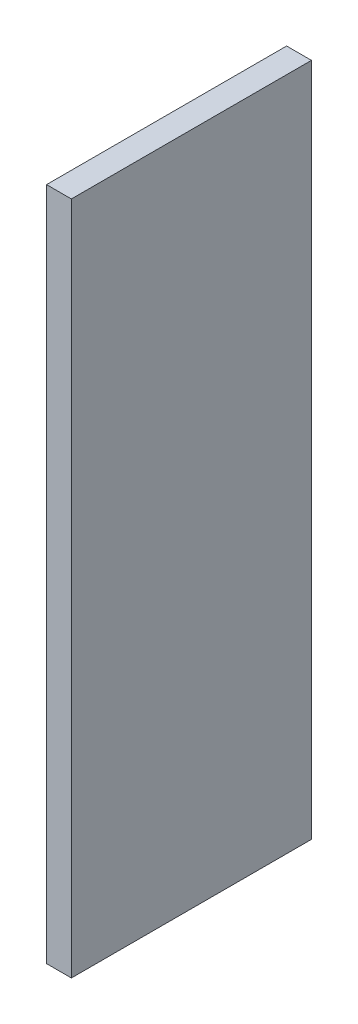
SolidWorks part; units mm, degrees
ref_plane "Front Plane" through (0, 0, 0) normal (0, 0, 1) x (1, 0, 0)
ref_plane "Top Plane" through (0, 0, 0) normal (0, 1, 0) x (1, 0, 0)
ref_plane "Right Plane" through (0, 0, 0) normal (1, 0, 0) x (0, 0, -1)
sketch "Sketch1" plane through (0, 0, 0) normal (1, 0, 0) x (0, 0, -1)
  line L1 (0, 0) -> (61.3842, 0)
  line L2 (0, 0) -> (0, 172.5092)
  line L3 (0, 172.5092) -> (61.3842, 172.5092)
  line L4 (61.3842, 0) -> (61.3842, 172.5092)
  dimension "D1" = 172.5092
  dimension "D2" = 61.3842
extrude "Boss-Extrude1" add sketch "Sketch1" along normal blind 6.35
